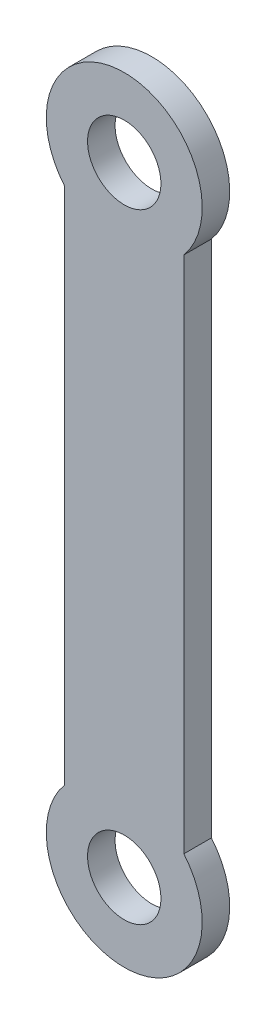
SolidWorks part; units mm, degrees
ref_plane "Plan de face" through (0, 0, 0) normal (0, 0, 1) x (1, 0, 0)
ref_plane "Plan de dessus" through (0, 0, 0) normal (0, 1, 0) x (1, 0, 0)
ref_plane "Plan de droite" through (0, 0, 0) normal (1, 0, 0) x (0, 0, -1)
sketch "Esquisse1" plane through (0, 0, 0) normal (0, 0, 1) x (1, 0, 0)
  line L0 (0, -24.5483) -> (0, 165.6418) construction
  line L1 (-13, 137.3107) -> (-13, 3.3184)
  line L2 (13, 3.3184) -> (13, 137.3107)
  circle A0 centre (0, 0) radius 8
  circle A1 centre (0, 0) radius 17
  circle A2 centre (0, 135) radius 17
  circle A3 centre (0, 135) radius 8
  dimension "D1" = 34
  dimension "D2" = 16
  dimension "D3" = 34
  dimension "D4" = 16
  dimension "D5" = 135
  dimension "D6" = 13
  dimension "D7" = 13
extrude "Boss.-Extru.1" add sketch "Esquisse1" along normal blind 6
